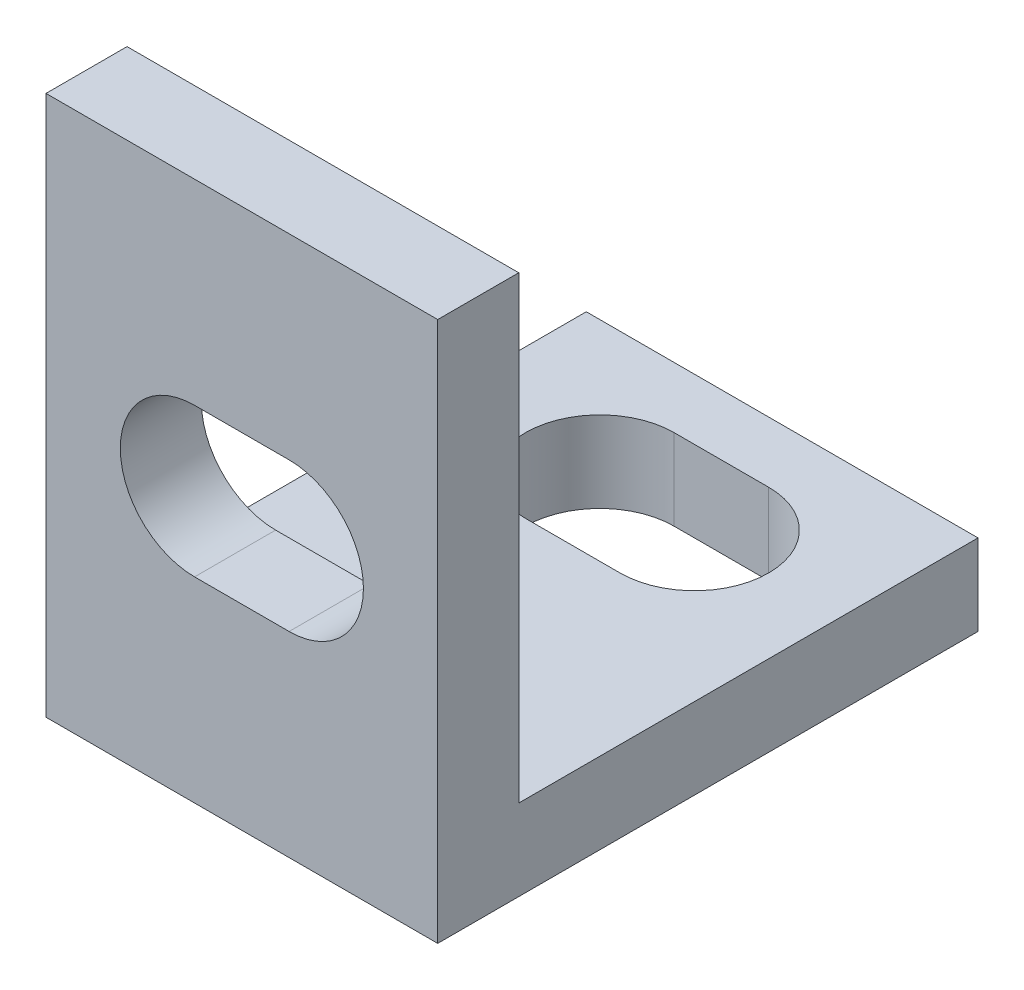
SolidWorks part; units mm, degrees
ref_plane "Front Plane" through (0, 0, 0) normal (0, 0, 1) x (1, 0, 0)
ref_plane "Top Plane" through (0, 0, 0) normal (0, 1, 0) x (1, 0, 0)
ref_plane "Right Plane" through (0, 0, 0) normal (1, 0, 0) x (0, 0, -1)
sketch "Sketch1" plane through (0, 0, 0) normal (1, 0, 0) x (0, 0, -1)
  line L0 (0, 20) -> (0, 0)
  line L1 (0, 0) -> (20, 0)
  line L2 (20, 0) -> (20, 3)
  line L3 (20, 3) -> (3, 3)
  line L4 (3, 3) -> (3, 20)
  line L5 (3, 20) -> (0, 20)
  dimension "D1" = 20
  dimension "D2" = 20
  dimension "D3" = 3
  dimension "D4" = 3
extrude "Boss-Extrude1" add sketch "Sketch1" against normal blind 14.5
sketch "Sketch2" plane through (0, 0, -3) normal (0, 0, -1) x (-1, 0, 0)
  line L0 (7.25, 20) -> (7.25, 3) construction
  line L1 (14.5, 20) -> (0, 20) construction
  line L2 (14.5, 3) -> (0, 3) construction
  line L3 (5.5, 10) -> (9, 10) construction
  line L4 (5.5, 12.75) -> (9, 12.75)
  line L5 (5.5, 7.25) -> (9, 7.25)
  line L7 (0, 3) -> (0, 20) construction
  line L8 (7.25, 10) -> (0, 10) construction
  arc A0 (5.5, 12.75) -> (5.5, 7.25) centre (5.5, 10) ccw
  arc A1 (9, 7.25) -> (9, 12.75) centre (9, 10) ccw
  point P8 (7.25, 10)
  dimension "D3" = 7.25
  dimension "D1" = 5.5
  dimension "D2" = 3.5
extrude "Cut-Extrude1" cut sketch "Sketch2" against normal through all contours L4 A1 L5 A0
sketch "Sketch3" plane through (0, 3, 0) normal (0, 1, 0) x (1, 0, 0)
  line L0 (-7.25, 3) -> (-7.25, 20) construction
  line L1 (-14.5, 3) -> (0, 3) construction
  line L2 (-14.5, 20) -> (0, 20) construction
  line L3 (-5.5, 15) -> (-9, 15) construction
  line L4 (-5.5, 12.25) -> (-9, 12.25)
  line L5 (-5.5, 17.75) -> (-9, 17.75)
  arc A0 (-5.5, 12.25) -> (-5.5, 17.75) centre (-5.5, 15) ccw
  arc A1 (-9, 17.75) -> (-9, 12.25) centre (-9, 15) ccw
  point P8 (-7.25, 15)
  dimension "D1" = 5.5
  dimension "D2" = 3.5
  dimension "D3" = 2.25
extrude "Cut-Extrude2" cut sketch "Sketch3" against normal through all
ref_plane "Plane1" through (-7.25, 0, 0) normal (1, 0, 0) x (0, 0, -1)
